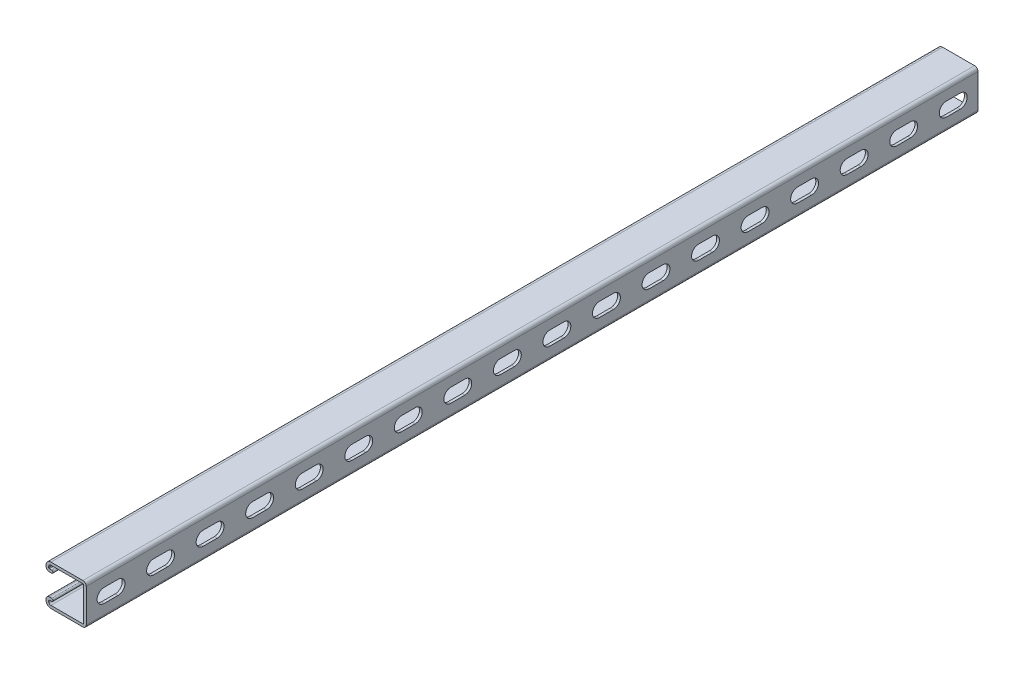
SolidWorks part; units mm, degrees
ref_plane "Front Plane" through (0, 0, 0) normal (0, 0, 1) x (1, 0, 0)
ref_plane "Top Plane" through (0, 0, 0) normal (0, 1, 0) x (1, 0, 0)
ref_plane "Right Plane" through (0, 0, 0) normal (1, 0, 0) x (0, 0, -1)
sketch "Sketch1" plane through (0, 0, 0) normal (0, 0, 1) x (1, 0, 0)
  line L0 (0, 0) -> (-41.275, 0) construction
  line L3 (-41.275, 20.6375) -> (0, 20.6375) construction
  line L4 (-41.275, 20.6375) -> (-41.275, -20.6375) construction
  line L5 (-41.275, -20.6375) -> (0, -20.6375) construction
  line L6 (0, 20.6375) -> (0, -20.6375) construction
  line L7 (-36.2267, 20.6375) -> (-3.4607, 20.6375)
  line L8 (0, 17.1767) -> (0, -17.1767)
  line L9 (-2.794, -17.1767) -> (-2.794, 17.1767)
  line L10 (-3.4608, 17.8435) -> (-36.2267, 17.8435)
  line L11 (-41.275, 15.5892) -> (-41.275, 14.5732)
  line L12 (-37.8142, 11.1125) -> (-35.5346, 11.1125)
  line L14 (-35.5346, 13.9065) -> (-37.8142, 13.9065)
  line L15 (-38.481, 14.5732) -> (-38.481, 15.5892)
  line L16 (-38.481, -14.5733) -> (-38.481, -15.5893)
  line L17 (-35.5346, -13.9065) -> (-37.8142, -13.9065)
  line L18 (-37.8142, -11.1125) -> (-35.5346, -11.1125)
  line L19 (-41.275, -15.5893) -> (-41.275, -14.5733)
  line L20 (-3.4607, -17.8435) -> (-36.2267, -17.8435)
  line L21 (-36.2267, -20.6375) -> (-3.4607, -20.6375)
  line L22 (-2.794, -20.6375) -> (-2.794, 20.6375) construction
  arc A1 (0, 17.1767) -> (-3.4607, 20.6375) centre (-3.4607, 17.1767) ccw
  arc A2 (-2.794, 17.1767) -> (-3.4608, 17.8435) centre (-3.4607, 17.1767) ccw
  arc A4 (-36.2267, 20.6375) -> (-41.275, 15.5892) centre (-36.2267, 15.5892) ccw
  arc A5 (-41.275, 14.5732) -> (-37.8142, 11.1125) centre (-37.8142, 14.5732) ccw
  arc A6 (-35.5346, 11.1125) -> (-35.5346, 13.9065) centre (-35.5346, 12.5095) ccw
  arc A7 (-37.8142, 13.9065) -> (-38.481, 14.5732) centre (-37.8142, 14.5732) cw
  arc A8 (-38.481, 15.5892) -> (-36.2267, 17.8435) centre (-36.2267, 15.5892) cw
  arc A9 (-38.481, -15.5893) -> (-36.2267, -17.8435) centre (-36.2267, -15.5893) ccw
  arc A10 (-37.8142, -13.9065) -> (-38.481, -14.5733) centre (-37.8142, -14.5733) ccw
  arc A11 (-35.5346, -11.1125) -> (-35.5346, -13.9065) centre (-35.5346, -12.5095) cw
  arc A12 (-41.275, -14.5733) -> (-37.8142, -11.1125) centre (-37.8142, -14.5733) cw
  arc A13 (-36.2267, -20.6375) -> (-41.275, -15.5893) centre (-36.2267, -15.5893) cw
  arc A14 (-2.794, -17.1767) -> (-3.4607, -17.8435) centre (-3.4607, -17.1767) cw
  arc A15 (0, -17.1767) -> (-3.4607, -20.6375) centre (-3.4607, -17.1767) cw
  point P24 (0, 20.6375)
  point P65 (-2.794, 0)
  dimension "D1" = 3.4608
  dimension "D2" = 5.0482
  dimension "D3" = 3.4608
  dimension "Ht." = 41.275
  dimension "Wd." = 41.275
  dimension "Thk." = 2.794
  dimension "D4" = 9.525
  dimension "D5" = 7.1374
extrude "Boss-Extrude1" add sketch "Sketch1" against normal blind 914.4
sketch "Sketch3" plane through (0, 0, 0) normal (1, 0, 0) x (0, 0, -1)
  line L0 (0, 0) -> (914.4, 0) construction
  point P2 (101.6, 0)
  point P3 (812.8, 0)
  dimension "D1" = 101.6
  dimension "D2" = 101.6
  dimension "D3" = 914.4
sketch "Sketch2" plane through (0, 0, 0) normal (1, 0, 0) x (0, 0, -1)
  line L0 (18.2562, 0) -> (32.5437, 0) construction
  line L1 (18.2562, 7.1437) -> (32.5437, 7.1437)
  line L2 (18.2562, -7.1437) -> (32.5437, -7.1437)
  line L3 (18.2562, 0) -> (0, 0) construction
  line L4 (25.4, 0) -> (76.2, 0) construction
  line L5 (0, -17.1767) -> (0, 17.1767) construction
  arc A0 (18.2562, 7.1437) -> (18.2562, -7.1437) centre (18.2562, 0) ccw
  arc A1 (32.5437, -7.1437) -> (32.5437, 7.1437) centre (32.5437, 0) ccw
  point P3 (25.4, 0)
  dimension "Slot Lg." = 28.575
  dimension "D2" = 25.4
  dimension "Slot Wd." = 14.2875
  dimension "Slot Ctr." = 50.8
  dimension "Hole to End" = 11.1125
extrude "Cut-Extrude1" cut sketch "Sketch2" against normal up to vertex (2.794 mm away) up to point (-2.794, 0, 0)
pattern_linear "LPattern1" count 18 spacing 50.8 along (0, 0, 1) of "Cut-Extrude1"
equation "\"D1@LPattern1\" = \"Slot Ctr.@Sketch2\""
equation "\"Hole Count@LPattern1\" = \"Lg.@Boss-Extrude1\" / \"D1@LPattern1\""
equation "\"D3@Sketch3\" = \"Lg.@Boss-Extrude1\""
